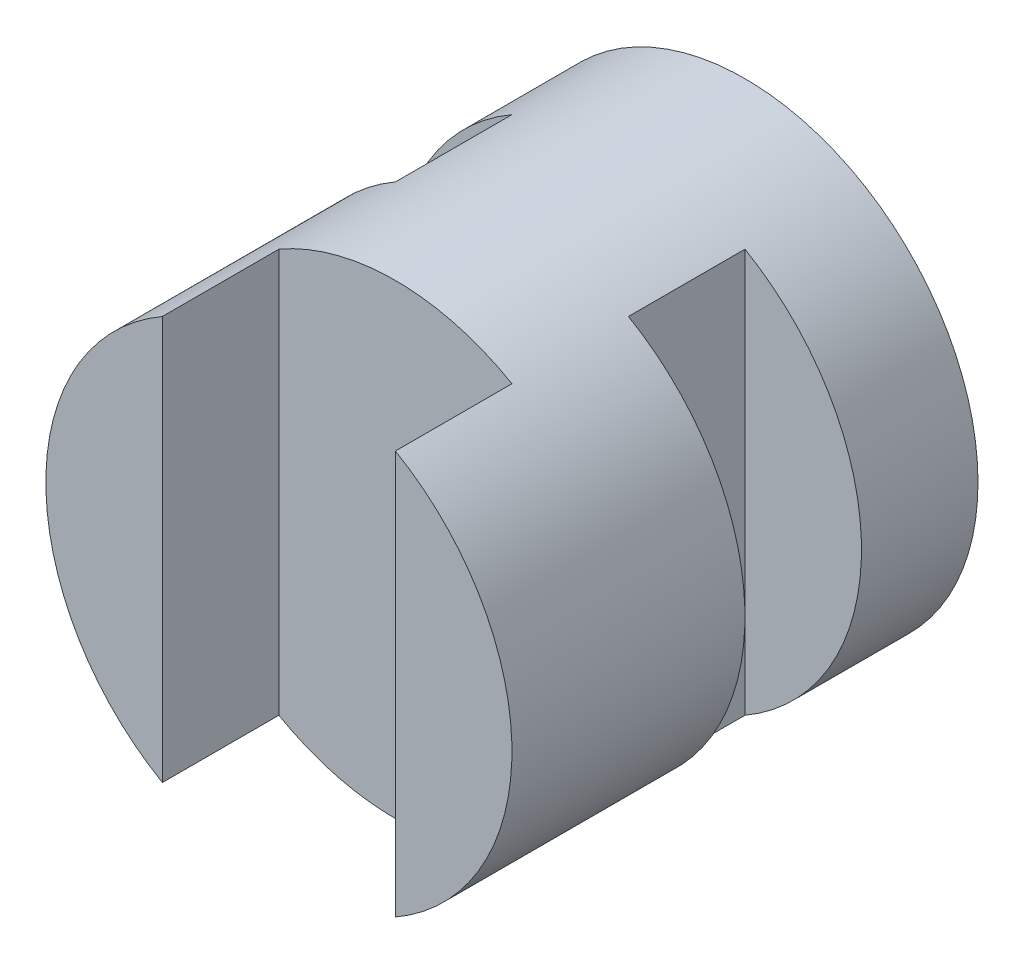
SolidWorks part; units mm, degrees
ref_plane "Front" through (0, 0, 0) normal (0, 0, 1) x (1, 0, 0)
ref_plane "Top" through (0, 0, 0) normal (0, 1, 0) x (1, 0, 0)
ref_plane "Right" through (0, 0, 0) normal (1, 0, 0) x (0, 0, -1)
sketch "Sketch1" plane through (0, 0, 0) normal (0, 0, 1) x (1, 0, 0)
  circle A0 centre (0, 0) radius 2
  dimension "D1" = 4
extrude "Boss-Extrude1" add sketch "Sketch1" along normal blind 4
sketch "Sketch2" plane through (0, 0, 0) normal (0, 1, 0) x (1, 0, 0)
  line L0 (-2, 0) -> (-2, -4) construction
  line L1 (-2, -1) -> (-1, -1)
  line L2 (-2, -1) -> (-2, -2)
  line L3 (-2, -2) -> (-1, -2)
  line L4 (-1, -1) -> (-1, -2)
  line L5 (2, 0) -> (-2, 0) construction
  line L6 (-2, -4) -> (2, -4) construction
  line L8 (2, -1) -> (2, -2)
  line L9 (2, -2) -> (1, -2)
  line L10 (1, -1) -> (1, -2)
  line L11 (-1, -4) -> (1, -4)
  line L12 (-1, -4) -> (-1, -3)
  line L13 (-1, -3) -> (1, -3)
  line L14 (1, -4) -> (1, -3)
  line L18 (1, -1) -> (2, -1)
  dimension "D1" = 0
  dimension "D2" = 1
  dimension "D3" = 1
  dimension "D4" = 1
  dimension "D5" = 1
  dimension "D7" = 2
  dimension "D8" = 1
  dimension "D9" = 1
extrude "Cut-Extrude1" cut sketch "Sketch2" against normal mid plane 10
